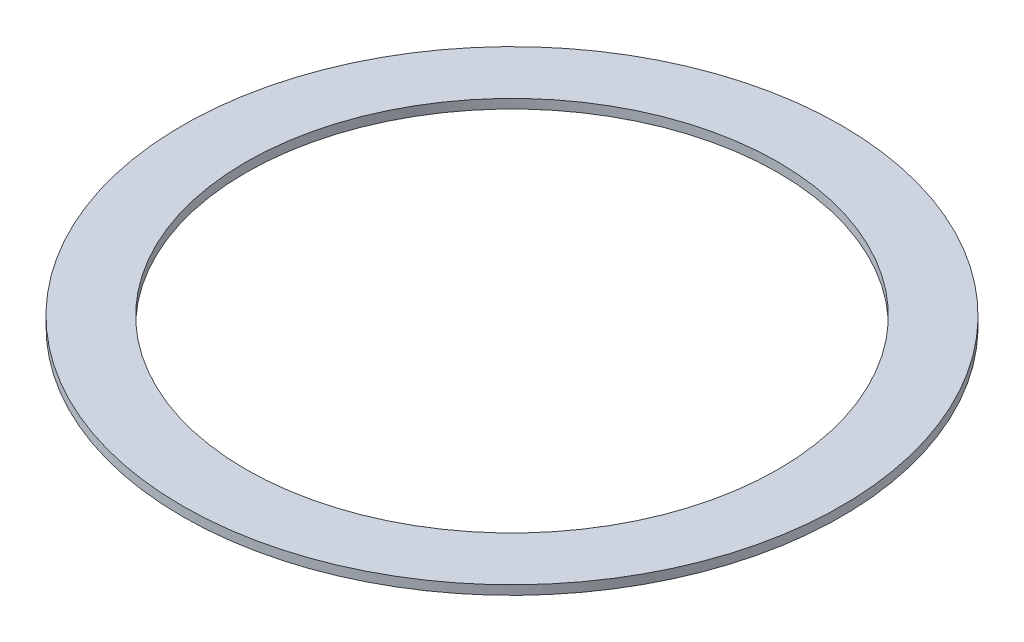
SolidWorks part; units mm, degrees
ref_plane "Front Plane" through (0, 0, 0) normal (0, 0, 1) x (1, 0, 0)
ref_plane "Top Plane" through (0, 0, 0) normal (0, 1, 0) x (1, 0, 0)
ref_plane "Right Plane" through (0, 0, 0) normal (1, 0, 0) x (0, 0, -1)
sketch "Sketch1" plane through (0, 0, 0) normal (0, 1, 0) x (1, 0, 0)
  circle A0 centre (0, 0) radius 250 construction
  circle A1 centre (0, 0) radius 290
  circle A2 centre (0, 0) radius 359.0961
  arc A3 (-13.137, -282.3258) -> (13.137, -282.3258) centre (0, -274.9187) ccw construction
  dimension "D1" = 500
extrude "Boss-Extrude1" add sketch "Sketch1" along normal blind 10
